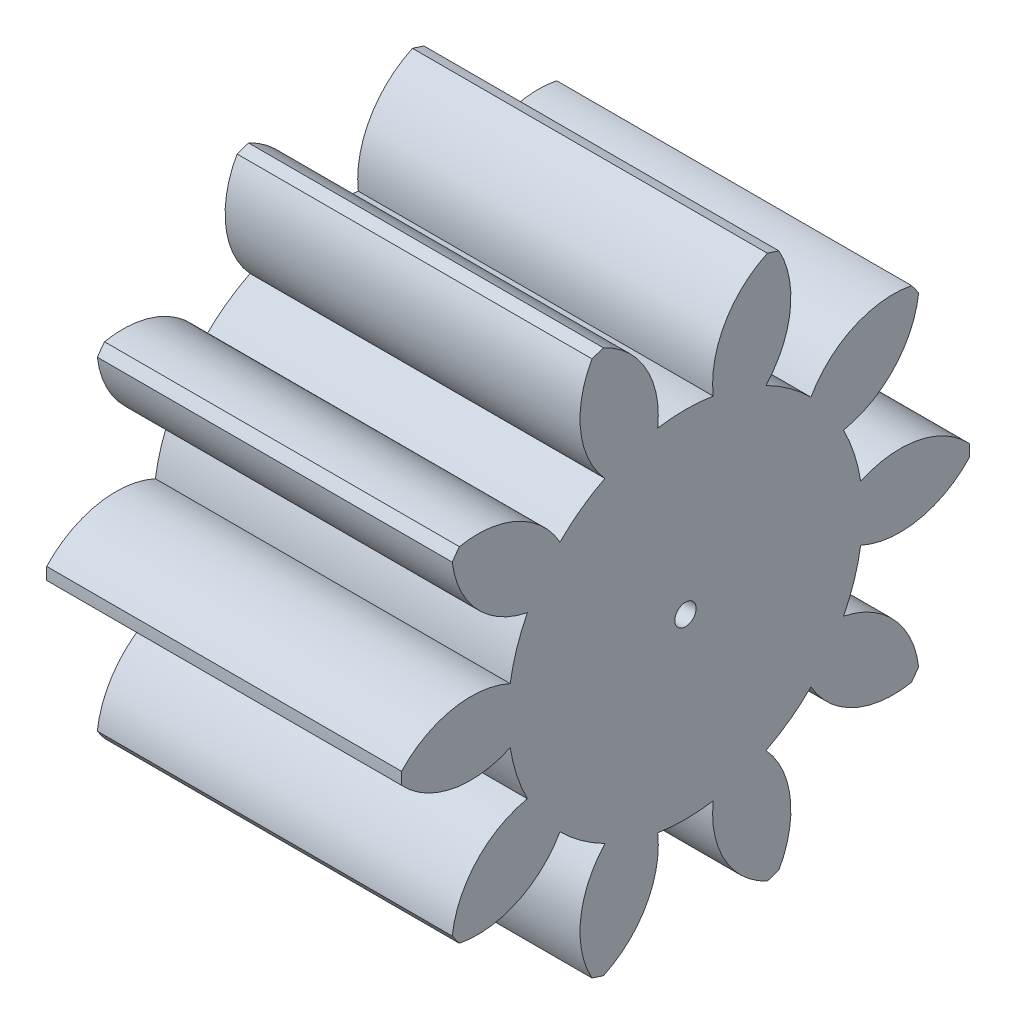
SolidWorks part; units mm, degrees
ref_plane "Plane1" through (0, 0, 0) normal (0, 0, 1) x (1, 0, 0)
ref_plane "Plane2" through (0, 0, 0) normal (0, 1, 0) x (1, 0, 0)
ref_plane "Plane3" through (0, 0, 0) normal (1, 0, 0) x (0, 0, -1)
other "Configuration Table"
sketch "HoldingSke" plane through (0, 0, 0) normal (0, 1, 0) x (1, 0, 0)
  line L0 (0, 0) -> (0.4924, -0.0868)
  line L1 (-15, 0) -> (100, 0) construction
  line L2 (0, 0) -> (-2.1039, 2.3779)
  line L3 (0, 0) -> (-11.863, 4.5341)
  line L4 (0, 0) -> (8.5048, 1.4996)
  line L5 (0, 0) -> (-46.8476, -17.4728)
  line L6 (0, 0) -> (-12.4344, -8.3896)
  line L7 (-2.1039, 2.3779) -> (8.6586, 51.2059)
  line L8 (-76.2, 54.61) -> (-76.1, 54.61)
  line L9 (-71.009, 38.7566) -> (-53.1078, 45.2721)
  line L10 (-76.2, 71.12) -> (104.1128, 71.12)
  line L11 (0, 0) -> (-15, 0)
  line L12 (-76.2, 101.6) -> (-76.133, 101.6)
  line L13 (24.9733, 27.94) -> (52.9518, 28.4284)
  line L14 (24.9733, 27.94) -> (24.9743, 27.94)
  line L15 (24.9733, 27.94) -> (100.4006, 29.5858)
  line L16 (-63.627, -2) -> (-12.827, -2)
  circle A0 centre (0, 0) radius 0.45
  circle A1 centre (0, 0) radius 7.499
  circle A2 centre (0, 0) radius 37.5
  circle A3 centre (0, 0) radius 0.45
  dimension "MHD" = 14.998
  dimension "Hub_dia" = 75
  dimension "Bore" = 0.9
  dimension "MBD" = 0.9
  dimension "Num_teeth" = 10
  dimension "Pitch" = 0.5
  dimension "Overall_len" = 50
  dimension "Show_teeth" = 10
  dimension "Thickness" = 15
  dimension "OAL" = 50.0001
  dimension "T_dim" = 0.1
  dimension "Ap" = 20
  dimension "H" = 19.05
  dimension "Pitch_radius" = 180.3128
  dimension "Width" = 15
  dimension "Backlash" = 0.067
  dimension "Addendum_fac" = 1
  dimension "Dedendum_fac" = 1.25
  dimension "Clearance_fac" = 0.25
  dimension "Dedendum_add" = 0.001
  dimension "Module" = 2
sketch "BasProSke" plane through (0, 0, 0) normal (0, 1, 0) x (1, 0, 0)
  line L0 (-10, 0) -> (60, 0) construction
  line L1 (0, 0) -> (0, 12)
  line L2 (0, 0) -> (15, 0)
  line L3 (15, 0) -> (15, 12)
  line L4 (15, 12) -> (0, 12)
  dimension "Thickness" = 15
  dimension "Diameter" = 24
revolve "Base-Revolve" add sketch "BasProSke" angle 360 about L0
sketch "TooCutSke" plane through (0, 0, 0) normal (1, 0, 0) x (0, 0, -1)
  line L1 (0, 0) -> (0, 107) construction
  line L2 (0, 0) -> (-1.6814, 9.8576) construction
  line L3 (0, 0) -> (-6.1153, 18.8209) construction
  line L4 (-1.6814, 9.8576) -> (-3.0576, 9.4105) construction
  arc A0 (1.1737, 7.4066) -> (-1.1737, 7.4066) centre (0, 0) ccw
  arc A1 (3.4979, 11.5054) -> (-3.4979, 11.5054) centre (0, 0) ccw
  circle A2 centre (0, 0) radius 10 construction
  circle A3 centre (0, 0) radius 9.3969 construction
  arc A4 (-1.1737, 7.4066) -> (-3.4979, 11.5054) centre (-5.1477, 7.8615) ccw
  arc A5 (3.4979, 11.5054) -> (1.1737, 7.4066) centre (5.1477, 7.8615) ccw
  dimension "Root_dia" = 14.998
  dimension "Overcut_dia" = 24.0508
  dimension "Pitch_dia" = 20
  dimension "Base_dia" = 18.7939
  dimension "Flank_rad" = 4
  dimension "Half_ang" = 18
  dimension "Half_CT" = 1.4471
extrude "ToothCut" cut sketch "TooCutSke" along normal through all
fillet "Breaks" [suppressed] radius 0.04
fillet "RootFillets" [suppressed] radius 0.501
pattern_circular "TeethCuts" count 10 every 36 about axis through (-10, 0, 0) along (1, 0, 0) of "ToothCut", "RootFillets", "Breaks"
sketch "HubNeaOneSke" plane through (0, 0, 0) normal (-1, 0, 0) x (0, 0, 1)
  circle A0 centre (0, 0) radius 7.499
  dimension "Diameter" = 14.998
extrude "HubNearOne" [suppressed] add sketch "HubNeaOneSke" along normal blind 35.0001
sketch "HubNeaBotSke" plane through (0, 0, 0) normal (-1, 0, 0) x (0, 0, 1)
  circle A0 centre (0, 0) radius 7.499
  dimension "Diameter" = 14.998
extrude "HubNearBoth" [suppressed] add sketch "HubNeaBotSke" along normal blind 17.5
ref_plane "FarPln" through (15, 0, 0) normal (1, 0, 0) x (0, 0, -1)
sketch "HubFarSke" plane through (15, 0, 0) normal (1, 0, 0) x (0, 0, -1)
  circle A0 centre (0, 0) radius 7.499
  dimension "Diameter" = 14.998
extrude "HubFar" [suppressed] add sketch "HubFarSke" along normal blind 17.5
sketch "BorSke" plane through (0, 0, 0) normal (1, 0, 0) x (0, 0, -1)
  circle A0 centre (0, 0) radius 0.45
  dimension "Diameter" = 0.9
extrude "Bore" cut sketch "BorSke" along normal mid plane 100.0001
sketch "KeySke" plane through (0, 0, 0) normal (1, 0, 0) x (0, 0, -1)
  line L0 (-0.05, 0) -> (-0.05, 0.55)
  line L1 (-0.05, 0.55) -> (0.05, 0.55)
  line L2 (0.05, 0.55) -> (0.05, 0)
  line L3 (0, 0) -> (0, 34) construction
  line L4 (-0.05, 0) -> (0.05, 0)
  dimension "Offset" = 0.55
  dimension "Width" = 0.1
extrude "Keyway" [suppressed] cut sketch "KeySke" along normal mid plane 100.0001
pattern_circular "Keyway2" [suppressed] count 2 every 90 about axis through (-10, 0, 0) along (1, 0, 0)
equation "' \"Module@HoldingSke\" = 6.35"
equation "' \"Num_teeth@HoldingSke\" = 12"
equation "' \"Ap@HoldingSke\" =  20"
equation "' \"Ap@HoldingSke\" = 20"
equation "' \"Width@HoldingSke\" = 0.5 * 25.4"
equation "' \"Hub_dia@HoldingSke\"= 1 * 25.4"
equation "' \"Hub_dia@HoldingSke\" = 1 * 25.4"
equation "' \"Overall_len@HoldingSke\" = 1.0 * 25.4"
equation "' \"Bore@HoldingSke\" = 0.75 * 25.4"
equation "' \"T_dim@HoldingSke\" = 0.1 * 25.4"
equation "' \"Width@KeySke\" = 0.25 * 25.4"
equation "' \"Show_teeth@HoldingSke\" = 13"
equation "' \"Backlash@HoldingSke\" = 0.009 * 25.4"
equation "' \"Addendum_fac@HoldingSke\" = 1.0"
equation "' \"Dedendum_fac@HoldingSke\" = 1.25"
equation "' \"Dedendum_add@HoldingSke\" = 0.00005 * 25.4"
equation "' \"Clearance_fac@HoldingSke\" = 0.25"
equation "\"Pitch@HoldingSke\" = 1 / \"Module@HoldingSke\""
equation "\"Overcut_dia@TooCutSke\" = (\"Num_teeth@HoldingSke\" + 2 * \"Addendum_fac@HoldingSke\") / \"Pitch@HoldingSke\" + 0.002 * 25.4"
equation "\"Pitch_dia@TooCutSke\" = \"Num_teeth@HoldingSke\" / \"Pitch@HoldingSke\""
equation "\"Base_dia@TooCutSke\" = \"Num_teeth@HoldingSke\" / \"Pitch@HoldingSke\" * cos((\"Ap@HoldingSke\"  * 3.14159265 / 180))"
equation "\"Root_dia@TooCutSke\" = (\"Num_teeth@HoldingSke\" + 2) / \"Pitch@HoldingSke\" - 2 * (\"Addendum_fac@HoldingSke\" + \"Dedendum_fac@HoldingSke\") / \"Pitch@HoldingSke\" - \"Dedendum_add@HoldingSke\" * 2"
equation "\"Half_ang@TooCutSke\" = 180 / \"Num_teeth@HoldingSke\""
equation "\"Half_CT@TooCutSke\" = \"Num_teeth@HoldingSke\" / \"Pitch@HoldingSke\" * sin((3.14159265 / 2 / \"Num_teeth@HoldingSke\")) / 2 - 7 * \"Backlash@HoldingSke\" / 4"
equation "\"Flank_rad@TooCutSke\" = \"Num_teeth@HoldingSke\" / \"Pitch@HoldingSke\" / 5"
equation "\"Radius@RootFillets\" = \"Clearance_fac@HoldingSke\" / \"Pitch@HoldingSke\" + \"Dedendum_add@HoldingSke\""
equation "\"Break_rad@Breaks\" = 0.02 / \"Pitch@HoldingSke\""
equation "\"Thickness@HoldingSke\" = \"Width@HoldingSke\""
equation "\"OAL@HoldingSke\" = \"Thickness@HoldingSke\""
equation "\"MHD@HoldingSke\" = (\"Num_teeth@HoldingSke\" + 2) / \"Pitch@HoldingSke\" - 2 * (\"Addendum_fac@HoldingSke\" + \"Dedendum_fac@HoldingSke\")  / \"Pitch@HoldingSke\" - \"Dedendum_add@HoldingSke\" * 2"
equation "\"MBD@HoldingSke\" = (\"Num_teeth@HoldingSke\" + 2) / \"Pitch@HoldingSke\" - 2 * (\"Addendum_fac@HoldingSke\" + \"Dedendum_fac@HoldingSke\")  / \"Pitch@HoldingSke\" - \"Dedendum_add@HoldingSke\" * 2 - 0.002 * 25.4"
equation "\"MHD@HoldingSke\" = ((sgn( \"MHD@HoldingSke\" - \"Hub_dia@HoldingSke\" )-1)*( \"MHD@HoldingSke\" - \"Hub_dia@HoldingSke\" ))/-2+ \"Hub_dia@HoldingSke\""
equation "\"MBD@HoldingSke\" = ((sgn( \"MBD@HoldingSke\" - \"Bore@HoldingSke\" )-1)*( \"MBD@HoldingSke\" - \"Bore@HoldingSke\" ))/-2+ \"Bore@HoldingSke\""
equation "\"OAL@HoldingSke\" = ((sgn( \"OAL@HoldingSke\" - \"Overall_len@HoldingSke\" )+1)*( \"OAL@HoldingSke\" - \"Overall_len@HoldingSke\" ))/2 + \"Overall_len@HoldingSke\" + 0.000002 * 25.4"
equation "\"Num_teeth@TeethCuts\" = int( \"Show_teeth@HoldingSke\" ) + 1"
equation "\"Num_teeth@TeethCuts\" = ((sgn( \"Num_teeth@TeethCuts\" - \"Num_teeth@HoldingSke\" )-1)*( \"Num_teeth@TeethCuts\" - \"Num_teeth@HoldingSke\" ))/-2+ \"Num_teeth@HoldingSke\""
equation "\"Num_teeth@TeethCuts\" = ((sgn( \"Num_teeth@TeethCuts\" - 2.0)+1)*( \"Num_teeth@TeethCuts\" - 2.0))/2 +2.0"
equation "\"Angle@TeethCuts\" = 360.0 / \"Num_teeth@HoldingSke\""
equation "\"Diameter@BasProSke\" = (\"Num_teeth@HoldingSke\" + 2 * \"Addendum_fac@HoldingSke\") / \"Pitch@HoldingSke\""
equation "\"Thickness@BasProSke\"  = \"Thickness@HoldingSke\""
equation "' \"Fillet_rad@BasProSke\" =  \"Thickness@HoldingSke\" * 0.05"
equation "' \"Fillet_rad@BasProSke\" = \"Thickness@HoldingSke\" * 0.05"
equation "\"MHD@HoldingSke\" = ((sgn( \"MHD@HoldingSke\" - \"Root_dia@TooCutSke\" )-1)*( \"MHD@HoldingSke\" - \"Root_dia@TooCutSke\" ))/-2+ \"Root_dia@TooCutSke\""
equation "\"Diameter@HubNeaOneSke\" = \"MHD@HoldingSke\""
equation "\"Length@HubNearOne\" = \"OAL@HoldingSke\" - \"Thickness@BasProSke\""
equation "\"Diameter@HubNeaBotSke\" = \"MHD@HoldingSke\""
equation "\"Length@HubNearBoth\" = ( \"OAL@HoldingSke\" - \"Thickness@BasProSke\" ) / 2.0"
equation "\"Thickness@FarPln\" = \"Thickness@BasProSke\""
equation "\"Diameter@HubFarSke\" = \"MHD@HoldingSke\""
equation "\"Length@HubFar\" = ( \"OAL@HoldingSke\" - \"Thickness@BasProSke\" ) / 2.0"
equation "\"Diameter@BorSke\" = \"MBD@HoldingSke\""
equation "\"D1@Bore\" = \"OAL@HoldingSke\" * 2.0"
equation "\"D1@Keyway\" = \"OAL@HoldingSke\" * 2.0"
equation "\"Offset@KeySke\" = \"T_dim@HoldingSke\" + \"MBD@HoldingSke\" / 2.0"
